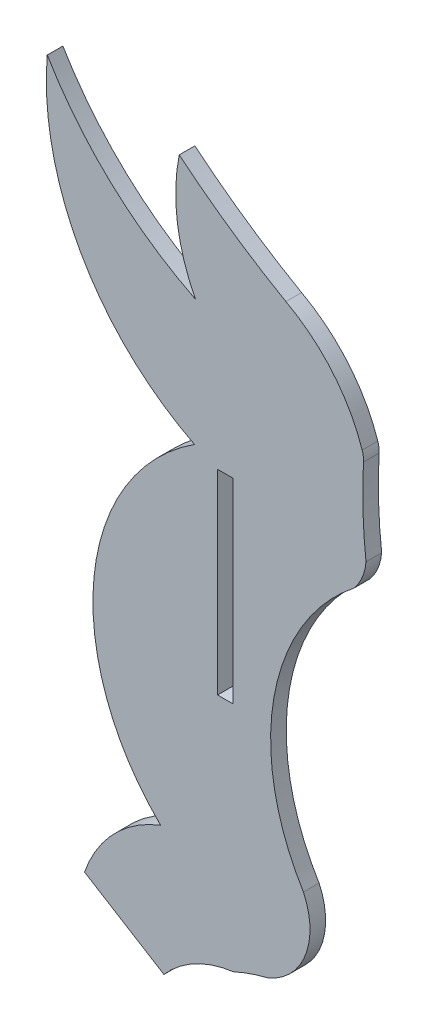
SolidWorks part; units mm, degrees
ref_plane "Front Plane" through (0, 0, 0) normal (0, 0, 1) x (1, 0, 0)
ref_plane "Top Plane" through (0, 0, 0) normal (0, 1, 0) x (1, 0, 0)
ref_plane "Right Plane" through (0, 0, 0) normal (1, 0, 0) x (0, 0, -1)
sketch "Sketch1" plane through (0, 0, 0) normal (0, 0, 1) x (1, 0, 0)
  line L1 (1.524, -174.0497) -> (0, -174.0497)
  line L2 (1.524, -174.0497) -> (1.524, -193.0997)
  line L3 (1.524, -193.0997) -> (0, -193.0997)
  line L4 (0, -174.0497) -> (0, -193.0997)
  line L5 (-12.9684, -214.5331) -> (-5.231, -219.3082)
  arc A0 (-2.2542, -173.0728) -> (-16.6029, -147.3789) centre (9.662, -149.5648) cw
  arc A1 (-16.6029, -147.3789) -> (-2.165, -160.7622) centre (13.3466, -129.5489) ccw
  arc A2 (-2.165, -160.7622) -> (-3.7385, -149.3734) centre (13.3537, -152.815) cw
  arc A3 (-3.7385, -149.3734) -> (6.6646, -156.5606) centre (43.2468, -92.4867) ccw
  arc A4 (6.6646, -156.5606) -> (14.0945, -165.3776) centre (-0.7957, -170.3862) cw
  arc A5 (14.2232, -166.3279) -> (14.4684, -174.622) centre (63.0676, -169.0343) ccw
  arc A6 (14.4684, -174.622) -> (13.3114, -177.4142) centre (9.5528, -174.221) cw
  arc A7 (13.3114, -177.4142) -> (8.3663, -205.5458) centre (26.6767, -194.2641) ccw
  arc A8 (8.3663, -205.5458) -> (4.9113, -214.5273) centre (2.372, -208.3952) cw
  arc A9 (4.9113, -214.5273) -> (1.524, -215.7006) centre (9.3836, -232.9152) ccw
  arc A10 (-5.231, -219.3082) -> (1.524, -215.7006) centre (2.8691, -226.3471) cw
  arc A12 (14.2232, -166.3279) -> (14.0945, -165.3776) centre (11.687, -166.1874) ccw
  arc A14 (-2.2542, -173.0728) -> (-5.5486, -206.8745) centre (9.5545, -191.2851) ccw
  arc A15 (-5.5486, -206.8745) -> (-12.9684, -214.5331) centre (-1.0563, -218.6503) ccw
extrude "Boss-Extrude1" add sketch "Sketch1" along normal blind 1.524
